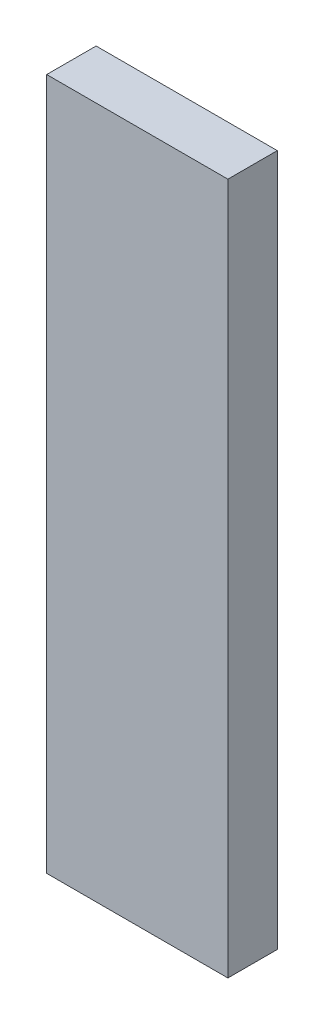
SolidWorks part; units mm, degrees
material "Oak"
ref_plane "Front Plane" through (0, 0, 0) normal (0, 0, 1) x (1, 0, 0)
ref_plane "Top Plane" through (0, 0, 0) normal (0, 1, 0) x (1, 0, 0)
ref_plane "Right Plane" through (0, 0, 0) normal (1, 0, 0) x (0, 0, -1)
sketch "Sketch1" plane through (0, 0, 0) normal (0, 1, 0) x (1, 0, 0)
  line L1 (-69.85, -19.05) -> (69.85, -19.05)
  line L2 (-69.85, -19.05) -> (-69.85, 19.05)
  line L3 (-69.85, 19.05) -> (69.85, 19.05)
  line L4 (69.85, -19.05) -> (69.85, 19.05)
  line L5 (-69.85, -19.05) -> (69.85, 19.05) construction
  line L6 (-69.85, 19.05) -> (69.85, -19.05) construction
  point P0 (0, 0)
  dimension "D1" = 38.1
  dimension "D2" = 139.7
extrude "Boss-Extrude1" add sketch "Sketch1" along normal blind 533.4 contours L1 L4 L3 L2
